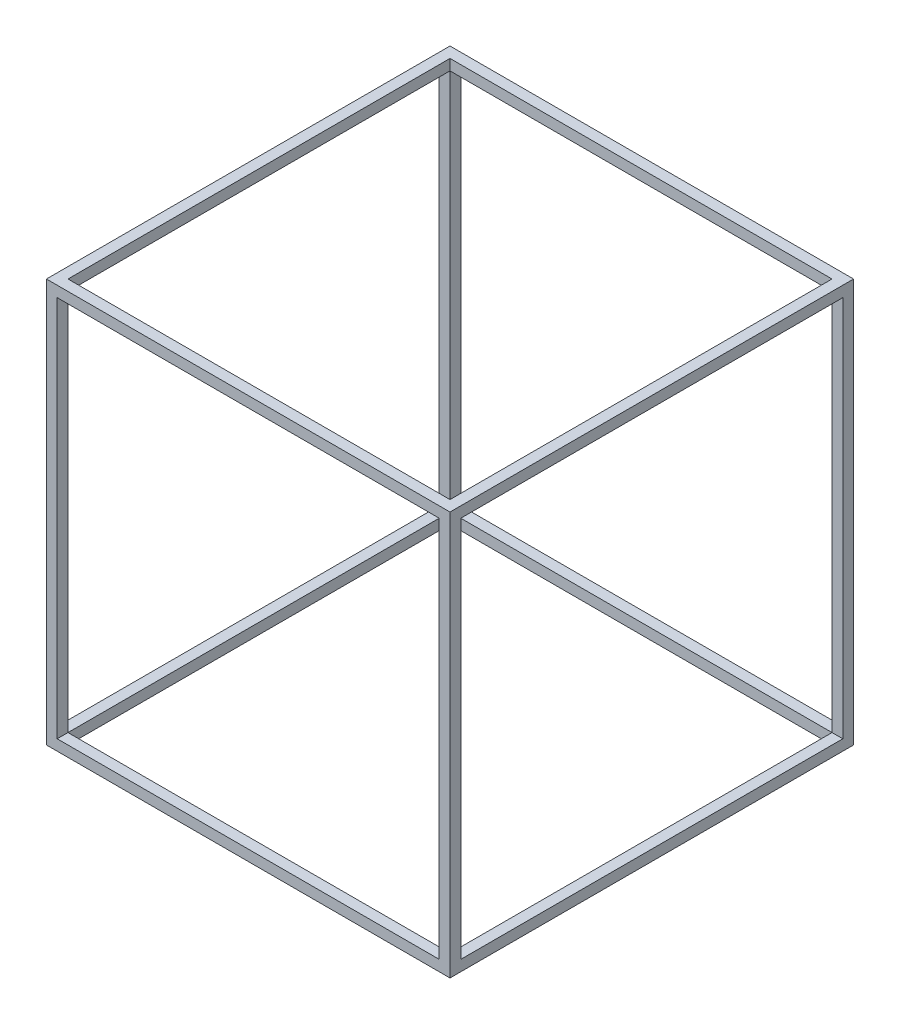
SolidWorks part; units mm, degrees
ref_plane "Front Plane" through (0, 0, 0) normal (0, 0, 1) x (1, 0, 0)
ref_plane "Top Plane" through (0, 0, 0) normal (0, 1, 0) x (1, 0, 0)
ref_plane "Right Plane" through (0, 0, 0) normal (1, 0, 0) x (0, 0, -1)
sketch "Sketch1" plane through (0, 0, 0) normal (0, 1, 0) x (1, 0, 0)
  line L1 (0, 0) -> (750, 0)
  line L2 (0, 0) -> (0, 750)
  line L3 (0, 750) -> (750, 750)
  line L4 (750, 0) -> (750, 750)
  line L5 (20, 20) -> (730, 20)
  line L6 (20, 20) -> (20, 730)
  line L7 (20, 730) -> (730, 730)
  line L8 (730, 20) -> (730, 730)
  dimension "D1" = 750
  dimension "D2" = 750
  dimension "D3" = 20
  dimension "D4" = 20
  dimension "D5" = 20
  dimension "D6" = 20
extrude "Boss-Extrude1" add sketch "Sketch1" along normal blind 20
sketch "Sketch2" plane through (0, 20, 0) normal (0, 1, 0) x (1, 0, 0)
  line L1 (0, 750) -> (20, 750)
  line L2 (0, 750) -> (0, 730)
  line L3 (0, 730) -> (20, 730)
  line L4 (20, 750) -> (20, 730)
  line L5 (750, 750) -> (730, 750)
  line L6 (750, 750) -> (750, 730)
  line L7 (750, 730) -> (730, 730)
  line L8 (730, 750) -> (730, 730)
  line L9 (0, 0) -> (20, 0)
  line L10 (0, 0) -> (0, 20)
  line L11 (0, 20) -> (20, 20)
  line L12 (20, 0) -> (20, 20)
  line L13 (750, 0) -> (730, 0)
  line L14 (750, 0) -> (750, 20)
  line L15 (750, 20) -> (730, 20)
  line L16 (730, 0) -> (730, 20)
extrude "Boss-Extrude2" add sketch "Sketch2" along normal blind 710
sketch "Sketch3" plane through (0, 730, 0) normal (0, 1, 0) x (1, 0, 0)
  line L0 (730, 750) -> (20, 750) construction
  line L1 (730, 730) -> (20, 730) construction
  line L2 (0, 730) -> (0, 20) construction
  line L3 (20, 730) -> (20, 20) construction
  line L4 (730, 20) -> (730, 730) construction
  line L5 (750, 20) -> (750, 730) construction
  line L6 (20, 20) -> (730, 20) construction
  line L7 (20, 0) -> (730, 0) construction
  line L8 (750, 0) -> (750, 20) construction
  line L9 (730, 0) -> (750, 0) construction
  line L10 (750, 730) -> (750, 750) construction
  line L11 (750, 750) -> (730, 750) construction
  line L12 (20, 750) -> (0, 750) construction
  line L13 (0, 750) -> (0, 730) construction
  line L14 (0, 20) -> (0, 0) construction
  line L15 (0, 0) -> (20, 0) construction
  line L16 (730, 750) -> (20, 750)
  line L17 (730, 730) -> (20, 730)
  line L18 (0, 730) -> (0, 20)
  line L19 (20, 730) -> (20, 20)
  line L20 (730, 20) -> (730, 730)
  line L21 (750, 20) -> (750, 730)
  line L22 (20, 20) -> (730, 20)
  line L23 (20, 0) -> (730, 0)
  line L24 (750, 0) -> (750, 20)
  line L25 (730, 0) -> (750, 0)
  line L26 (750, 730) -> (750, 750)
  line L27 (750, 750) -> (730, 750)
  line L28 (20, 750) -> (0, 750)
  line L29 (0, 750) -> (0, 730)
  line L30 (0, 20) -> (0, 0)
  line L31 (0, 0) -> (20, 0)
extrude "Boss-Extrude3" add sketch "Sketch3" along normal blind 20
